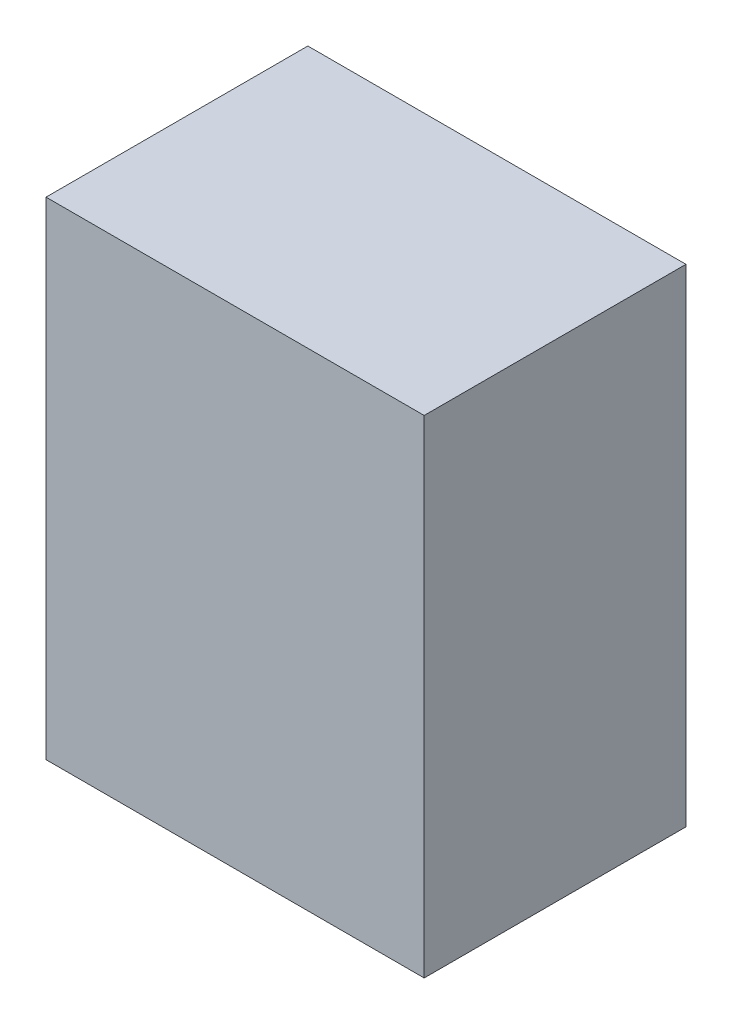
SolidWorks part; units mm, degrees
ref_plane "Front Plane" through (0, 0, 0) normal (0, 0, 1) x (1, 0, 0)
ref_plane "Top Plane" through (0, 0, 0) normal (0, 1, 0) x (1, 0, 0)
ref_plane "Right Plane" through (0, 0, 0) normal (1, 0, 0) x (0, 0, -1)
sketch "Sketch1" plane through (0, 0, 0) normal (0, 1, 0) x (1, 0, 0)
  line L1 (-330.2, -228.6) -> (330.2, -228.6)
  line L2 (-330.2, -228.6) -> (-330.2, 228.6)
  line L3 (-330.2, 228.6) -> (330.2, 228.6)
  line L4 (330.2, -228.6) -> (330.2, 228.6)
  line L5 (-330.2, -228.6) -> (330.2, 228.6) construction
  line L6 (-330.2, 228.6) -> (330.2, -228.6) construction
  point P0 (0, 0)
  dimension "D1" = 660.4
  dimension "D2" = 457.2
extrude "Boss-Extrude1" add sketch "Sketch1" along normal mid plane 850.9
